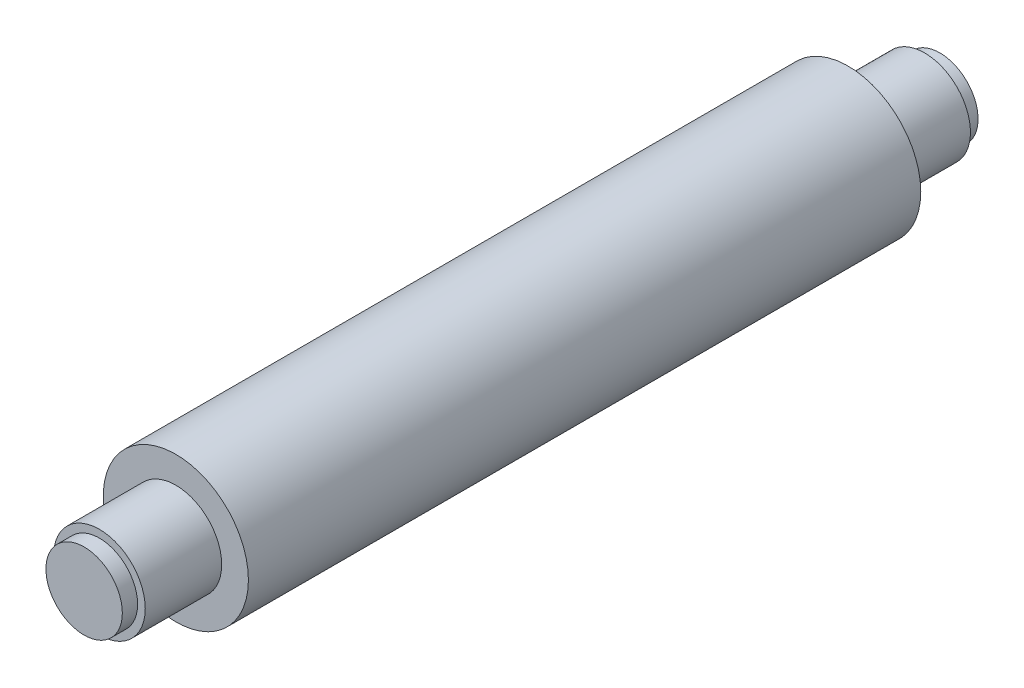
SolidWorks part; units mm, degrees
ref_plane "Front Plane" through (0, 0, 0) normal (0, 0, 1) x (1, 0, 0)
ref_plane "Top Plane" through (0, 0, 0) normal (0, 1, 0) x (1, 0, 0)
ref_plane "Right Plane" through (0, 0, 0) normal (1, 0, 0) x (0, 0, -1)
sketch "Sketch1" plane through (0, 0, 0) normal (0, 0, 1) x (1, 0, 0)
  circle A0 centre (0, 0) radius 47.5
  dimension "D1" = 95
extrude "Boss-Extrude1" add sketch "Sketch1" along normal blind 440
sketch "Sketch2" plane through (0, 0, 0) normal (0, 0, -1) x (-1, 0, 0)
  circle A0 centre (0, 0) radius 30
extrude "Boss-Extrude2" add sketch "Sketch2" along normal blind 50
sketch "Sketch3" plane through (0, 0, 440) normal (0, 0, 1) x (1, 0, 0)
  circle A0 centre (0, 0) radius 30
  dimension "D1" = 60
extrude "Boss-Extrude3" add sketch "Sketch3" along normal blind 50
sketch "Sketch4" plane through (0, 0, 490) normal (0, 0, 1) x (1, 0, 0)
  circle A0 centre (0, 0) radius 25
extrude "Boss-Extrude4" add sketch "Sketch4" along normal blind 10
sketch "Sketch5" plane through (0, 0, -50) normal (0, 0, -1) x (-1, 0, 0)
  circle A0 centre (0, 0) radius 25
  dimension "D1" = 50
extrude "Boss-Extrude5" add sketch "Sketch5" along normal blind 10
